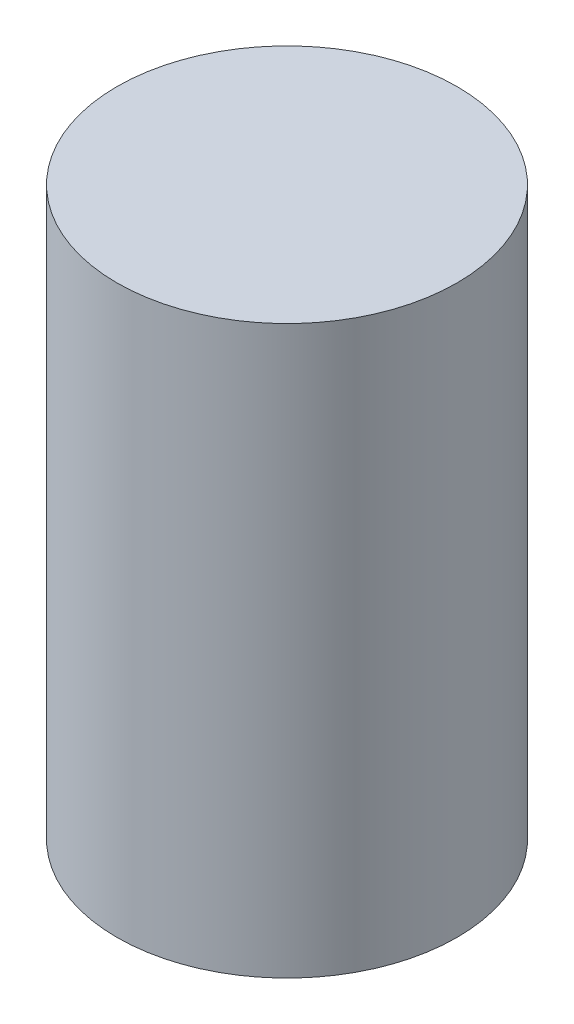
SolidWorks part; units mm, degrees
ref_plane "Alzado" through (0, 0, 0) normal (0, 0, 1) x (1, 0, 0)
ref_plane "Planta" through (0, 0, 0) normal (0, 1, 0) x (1, 0, 0)
ref_plane "Vista lateral" through (0, 0, 0) normal (1, 0, 0) x (0, 0, -1)
sketch "Croquis1" plane through (0, 0, 0) normal (0, 1, 0) x (1, 0, 0)
  circle A0 centre (0, 0) radius 3.81
  dimension "D1" = 7.62
extrude "Saliente-Extruir1" add sketch "Croquis1" along normal blind 12.7
